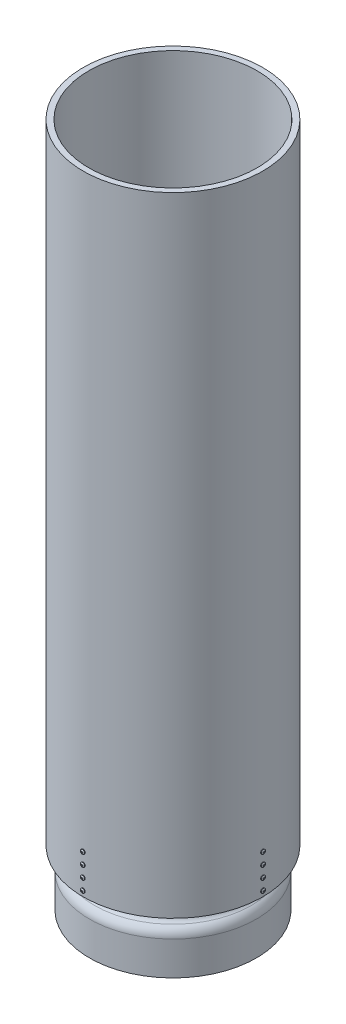
SolidWorks part; units mm, degrees
ref_plane "Front" through (0, 0, 0) normal (0, 0, 1) x (1, 0, 0)
ref_plane "Top" through (0, 0, 0) normal (0, 1, 0) x (1, 0, 0)
ref_plane "Right" through (0, 0, 0) normal (1, 0, 0) x (0, 0, -1)
sketch "Sketch2" plane through (0, 0, 0) normal (0, 0, 1) x (1, 0, 0)
  line L0 (0, -96.4651) -> (0, 112.46) construction
  line L1 (-177.8, 0) -> (-177.8, 76.2)
  line L2 (-190.5, 127) -> (-190.5, 1549.4)
  line L3 (-190.5, 1549.4) -> (-203.2, 1549.4)
  line L4 (-203.2, 1549.4) -> (-203.2, 127)
  line L5 (-203.2, 127) -> (-190.5, 127)
  line L6 (-177.8, 0) -> (-188.8998, 0)
  line L7 (-188.8998, 0) -> (-188.8998, 76.2)
  line L10 (0, 79.375) -> (0, 76.2)
  line L12 (-169.8625, 111.8308) -> (-169.8625, 228.6)
  line L13 (-169.8625, 228.6) -> (-158.7627, 228.6)
  line L14 (-158.7627, 228.6) -> (-158.7627, 111.8308)
  arc A0 (-177.6184, 97.3145) -> (-188.8998, 76.2) centre (-163.4998, 76.2) ccw
  arc A2 (-170.0441, 90.7163) -> (-177.8, 76.2) centre (-160.3375, 76.2) ccw
  arc A3 (-170.0441, 90.7163) -> (-158.7627, 111.8308) centre (-184.1627, 111.8308) ccw
  arc A4 (-177.6184, 97.3145) -> (-169.8625, 111.8308) centre (-187.325, 111.8308) ccw
  dimension "D9" = 17.4625
  dimension "D10" = 76.2
  dimension "D8" = 25.4
  dimension "D13" = 25.4
  dimension "D14" = 17.4625
  dimension "D1" = 1549.4
  dimension "D2" = 11.0998
  dimension "D3" = 12.7
  dimension "D4" = 406.4
  dimension "D5" = 355.6
  dimension "D6" = 127
  dimension "D7" = 11.0998
  dimension "D11" = 228.6
  dimension "D12" = 20.6375
revolve "Revolve1" add sketch "Sketch2" angle 360 about L0
sketch "Sketch3" plane through (0, 127, 0) normal (0, -1, 0) x (1, 0, 0)
  line L0 (-9.525, 190.2617) -> (-9.525, 169.5952)
  line L1 (9.525, 190.2617) -> (9.525, 169.5952)
  circle A0 centre (0, 0) radius 169.8625 construction
  arc A1 (9.525, 169.5952) -> (-9.525, 169.5952) centre (0, 0) ccw
  circle A2 centre (0, 0) radius 190.5 construction
  arc A3 (9.525, 190.2617) -> (-9.525, 190.2617) centre (0, 0) ccw
  point P5 (0, 169.8625)
  dimension "D1" = 19.05
extrude "Boss-Extrude1" add sketch "Sketch3" against normal blind 101.6 separate body
ref_plane "Plane1" through (0, 0, 203.2) normal (0, 0, 1) x (1, 0, 0)
sketch "Sketch4" plane through (0, 0, 203.2) normal (0, 0, 1) x (1, 0, 0)
  line L0 (-9.525, 228.6) -> (-9.525, 127) construction
  line L1 (-9.525, 228.6) -> (-9.525, 127) construction
  line L2 (0, 165.1) -> (0, 190.5) construction
  line L3 (-9.525, 177.8) -> (0, 177.8) construction
  line L4 (0, 215.9) -> (0, 190.5) construction
  line L5 (0, 165.1) -> (0, 139.7) construction
  line L8 (0, 165.1) -> (18.0235, 165.1) construction
  line L9 (0, 177.8) -> (18.0235, 177.8) construction
  line L10 (18.0235, 177.8) -> (18.0235, 165.1) construction
  line L11 (0, 139.7) -> (0, 127) construction
  line L12 (-9.525, 127) -> (9.525, 127) construction
  line L13 (0, 215.9) -> (0, 228.6) construction
  line L14 (9.525, 228.6) -> (-9.525, 228.6) construction
  circle A0 centre (0, 139.7) radius 2.5527
  circle A1 centre (0, 165.1) radius 2.5527
  circle A2 centre (0, 190.5) radius 2.5527
  circle A3 centre (0, 215.9) radius 2.5527
  dimension "D1" = 5.1054
  dimension "D2" = 12.7
  dimension "D3" = 25.4
extrude "Cut-Extrude1" cut sketch "Sketch4" against normal blind 25.4
pattern_circular "CirPattern1" count 4 over 360 about axis through (0, 0, 0) along (0, 1, 0) of bodies 111 105
pattern_circular "CirPattern2" count 4 over 360 about axis through (0, 127, 0) along (0, -1, 0) of "Cut-Extrude1"
sketch "Sketch6" plane through (0, 0, 0) normal (1, 0, 0) x (0, 0, -1)
  line L0 (-226.8447, 215.9) -> (-179.5553, 215.9) construction
  line L1 (-203.2, 127) -> (203.2, 127) construction
  line L2 (-203.2, 215.9) -> (-203.2, 211.1629)
  line L3 (-203.2, 211.1629) -> (-204.7875, 211.1629)
  line L4 (-203.2, 215.9) -> (-206.5782, 215.9)
  line L5 (-203.2, 213.3473) -> (-203.2, 193.0527) construction
  arc A1 (-206.5782, 215.9) -> (-204.7875, 211.1629) centre (-199.4171, 215.9) ccw
  point P12 (-203.2, 213.5314)
  dimension "D1" = 88.9
  dimension "D2" = 3.3782
  dimension "D3" = 9.4742
  dimension "D4" = 1.5875
revolve "Revolve2" add sketch "Sketch6" angle 360 about L0
ref_plane "Plane2" through (0, 0, 206.5782) normal (0, 0, 1) x (1, 0, 0)
sketch "Sketch7" plane through (0, 0, 206.5782) normal (0, 0, 1) x (1, 0, 0)
  line L0 (-4.7371, 215.9) -> (-2.3813, 215.9) construction
  line L1 (2.3813, 216.2969) -> (0.3969, 216.2969)
  line L2 (2.3813, 216.2969) -> (2.3813, 215.5031)
  line L3 (2.3813, 215.5031) -> (0.3969, 215.5031)
  line L4 (-2.3813, 216.2969) -> (-2.3813, 215.5031)
  line L5 (0.3969, 218.2812) -> (-0.3969, 218.2812)
  line L6 (0.3969, 218.2812) -> (0.3969, 216.2969)
  line L7 (0.3969, 213.5187) -> (-0.3969, 213.5187)
  line L8 (-0.3969, 218.2812) -> (-0.3969, 216.2969)
  line L9 (0, 220.6371) -> (0, 218.2812) construction
  line L10 (0, 218.2812) -> (0, 213.5187) construction
  line L11 (-2.3813, 215.9) -> (2.3813, 215.9) construction
  line L12 (0, 213.5187) -> (0, 211.1629) construction
  line L13 (-0.3969, 215.5031) -> (-0.3969, 213.5187)
  line L14 (-0.3969, 215.5031) -> (-2.3813, 215.5031)
  line L15 (0.3969, 215.5031) -> (0.3969, 213.5187)
  line L16 (-0.3969, 216.2969) -> (-2.3813, 216.2969)
  circle A0 centre (0, 215.9) radius 4.7371 construction
  point P8 (0, 215.9)
  point P13 (0, 215.9)
  dimension "D1" = 0.7937
  dimension "D2" = 0.7937
  dimension "D3" = 4.7625
  dimension "D4" = 4.7625
extrude "Cut-Extrude2" cut sketch "Sketch7" against normal blind 1.5875
pattern_linear "LPattern1" count 4 spacing 25.4 along (0, -1, 0) of bodies 115
pattern_circular "CirPattern3" count 4 over 360 about axis through (0, 0, 0) along (0, 1, 0) of bodies 116 118 117 115
